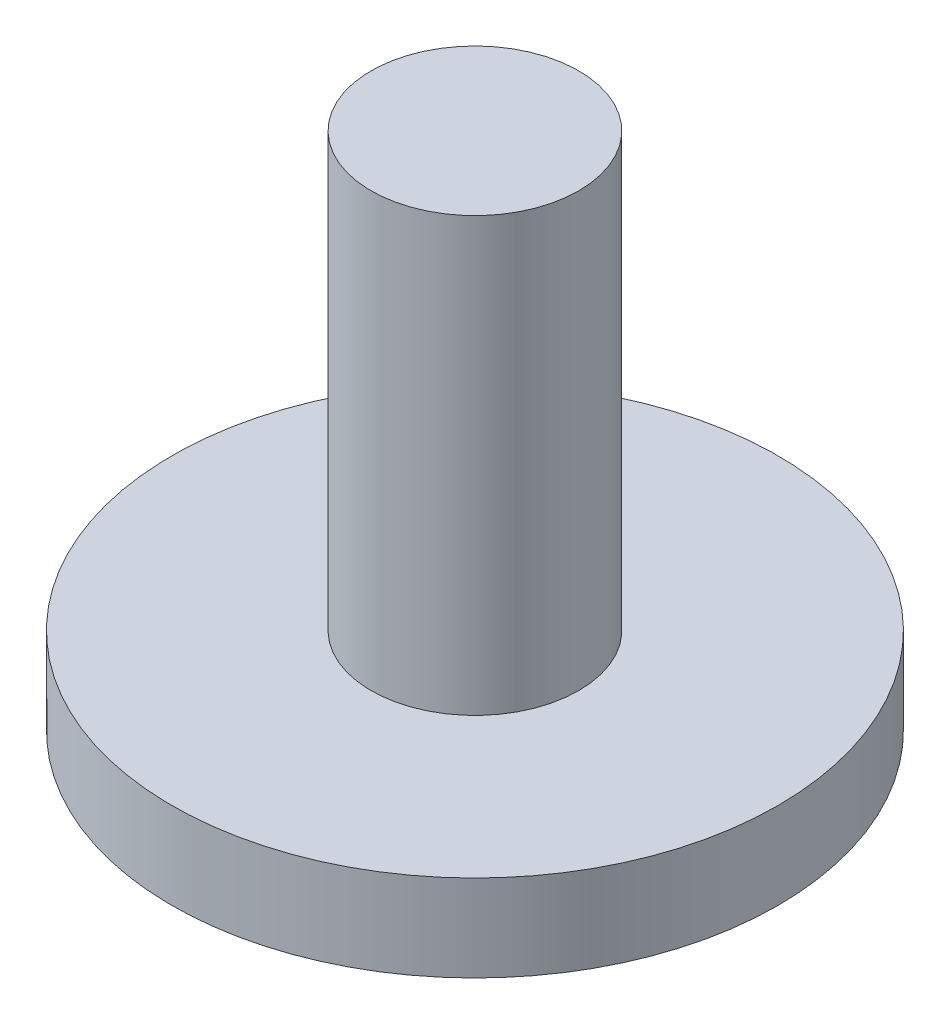
SolidWorks part; units mm, degrees
ref_plane "Front Plane" through (0, 0, 0) normal (0, 0, 1) x (1, 0, 0)
ref_plane "Top Plane" through (0, 0, 0) normal (0, 1, 0) x (1, 0, 0)
ref_plane "Right Plane" through (0, 0, 0) normal (1, 0, 0) x (0, 0, -1)
sketch "Sketch1" plane through (0, 0, 0) normal (0, 0, 1) x (1, 0, 0)
  line L0 (-404.386, 0) -> (19814.9133, 0) construction
  line L1 (0, -404.386) -> (0, 19814.9133) construction
  line L2 (0, 6) -> (2.4, 6)
  line L3 (2.4, 6) -> (2.4, -4)
  line L4 (2.4, -4) -> (7, -4)
  line L5 (7, -4) -> (7, -6)
  line L6 (7, -6) -> (0, -6)
  line L7 (0, -6) -> (0, 6)
  dimension "D1" = 2
  dimension "D2" = 10
  dimension "D3" = 7
  dimension "D4" = 2.4
revolve "Revolve1" add sketch "Sketch1" angle 360 about L1
